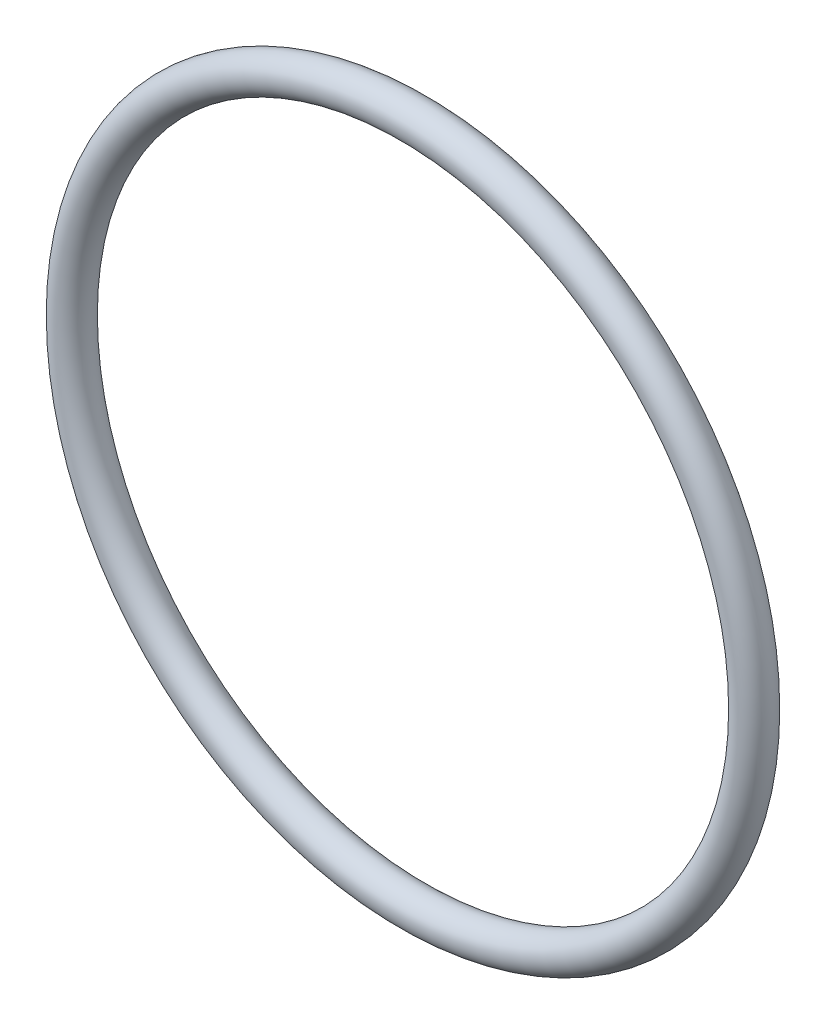
SolidWorks part; units mm, degrees
ref_plane "Front" through (0, 0, 0) normal (0, 0, 1) x (1, 0, 0)
ref_plane "Top" through (0, 0, 0) normal (0, 1, 0) x (1, 0, 0)
ref_plane "Right" through (0, 0, 0) normal (1, 0, 0) x (0, 0, -1)
sketch "Sketch1" plane through (0, 0, 0) normal (1, 0, 0) x (0, -1, 0)
  line L0 (0, -1.7653) -> (0, 1.7653) construction
  line L2 (-38.5851, 0) -> (38.5851, 0) construction
  line L3 (-31.5468, 0) -> (31.5468, 0) construction
  circle A0 centre (33.3121, 0) radius 1.7653
  point P9 (31.5468, 0)
  point P10 (35.0774, 0)
  point P13 (33.3121, 1.7653)
  point P14 (33.3121, -1.7653)
  dimension "Width" = 3.5306
  dimension "ID" = 63.0936
revolve "Revolve1" add sketch "Sketch1" angle 360 about L0
